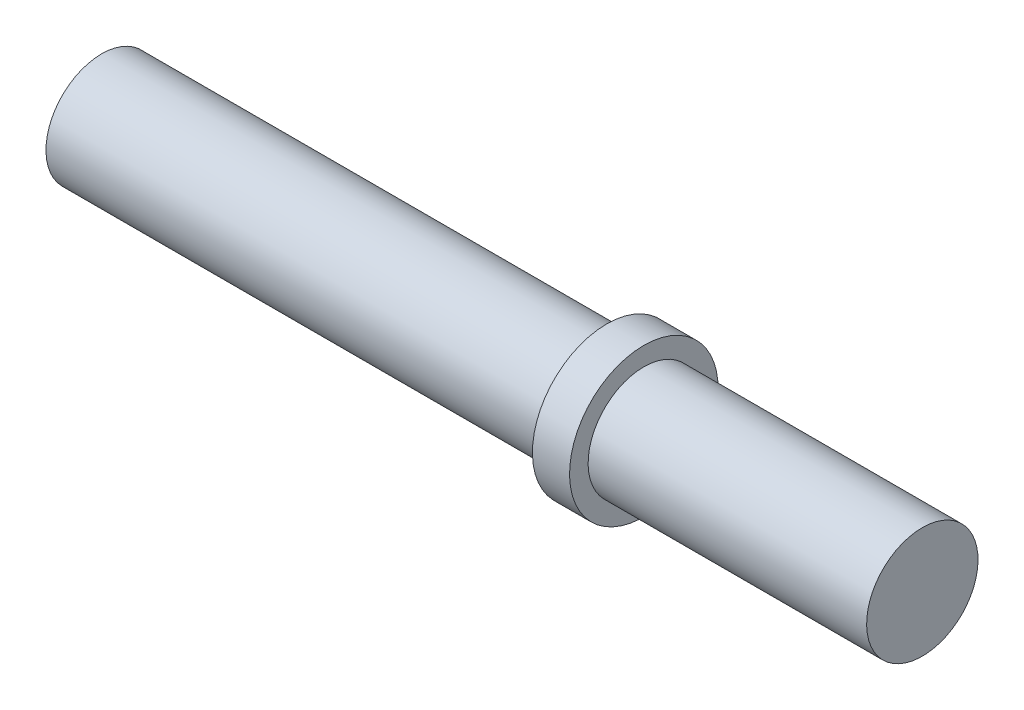
SolidWorks part; units mm, degrees
ref_plane "Front Plane" through (0, 0, 0) normal (0, 0, 1) x (1, 0, 0)
ref_plane "Top Plane" through (0, 0, 0) normal (0, 1, 0) x (1, 0, 0)
ref_plane "Right Plane" through (0, 0, 0) normal (1, 0, 0) x (0, 0, -1)
sketch "Sketch1" plane through (0, 0, 0) normal (0, 0, 1) x (1, 0, 0)
  line L0 (0, 3) -> (0, 0)
  line L1 (0, 0) -> (27.2, 0)
  line L2 (27.2, 0) -> (27.2, -1)
  line L3 (27.2, -1) -> (29.2, -1)
  line L4 (29.2, -1) -> (29.2, 0)
  line L5 (29.2, 0) -> (44.2, 0)
  line L6 (44.2, 0) -> (44.2, 3)
  line L7 (44.2, 3) -> (0, 3)
  dimension "D1" = 44.2
  dimension "D2" = 27.2
  dimension "D3" = 2
  dimension "D4" = 3
  dimension "D5" = 1
revolve "Revolve1" add sketch "Sketch1" angle 360 about L7
